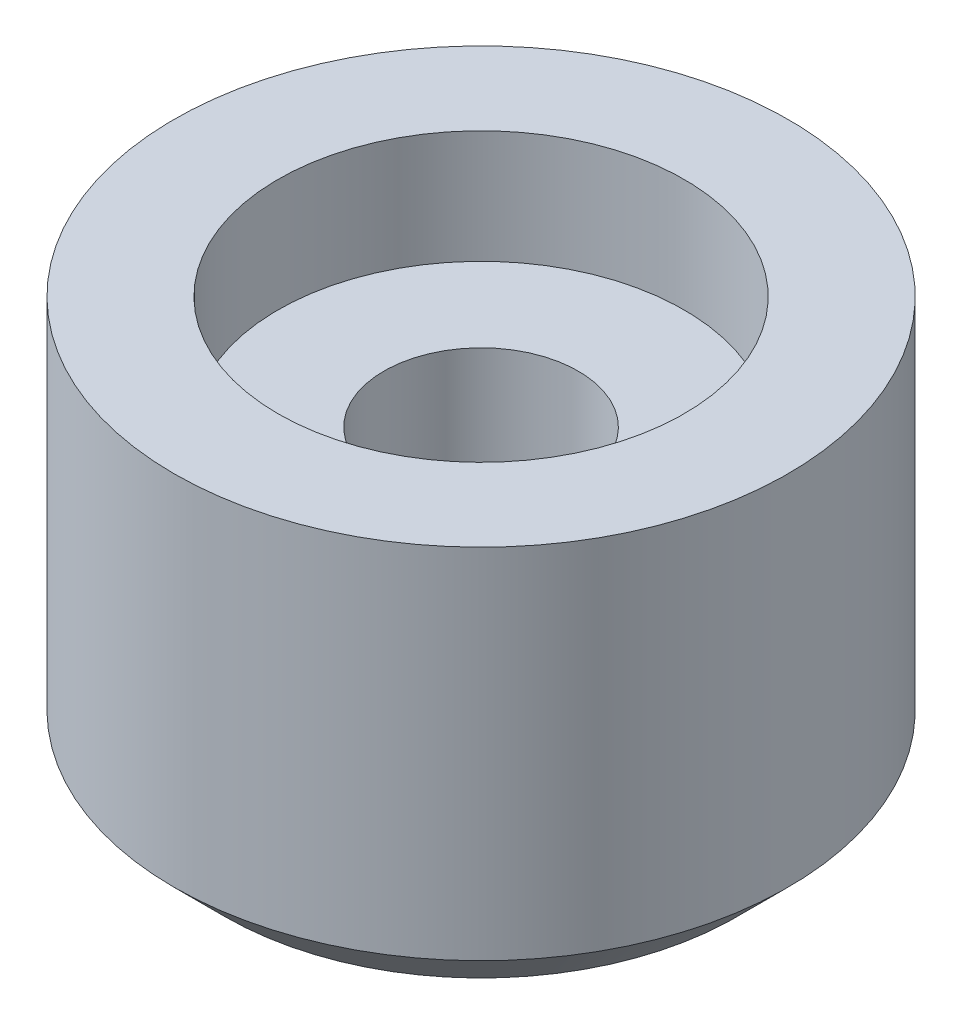
SolidWorks part; units mm, degrees
ref_plane "Front Plane" through (0, 0, 0) normal (0, 0, 1) x (1, 0, 0)
ref_plane "Top Plane" through (0, 0, 0) normal (0, 1, 0) x (1, 0, 0)
ref_plane "Right Plane" through (0, 0, 0) normal (1, 0, 0) x (0, 0, -1)
sketch "Sketch1" plane through (0, 0, 0) normal (0, 1, 0) x (1, 0, 0)
  circle A0 centre (0, 0) radius 6
  dimension "D1" = 12
extrude "Boss-Extrude1" add sketch "Sketch1" along normal blind 8
hole_wizard "CBORE for #6 Binding Head Machine Screw2" positions "Sketch2" profile "Sketch3" counterbore size "#6" standard "ANSI Inch" end condition through all
sketch "Sketch2" plane through (0, 8, 0) normal (0, 1, 0) x (1, 0, 0)
  point P0 (0, 0)
sketch "Sketch3" plane through (0, 8, 0) normal (1, 0, 0) x (0, 0, 1)
  line L0 (0, 0) -> (0, 8)
  line L1 (0, 8) -> (1.8986, 8)
  line L3 (1.8986, 8) -> (1.8986, 2.2098)
  line L4 (1.8986, 2.2098) -> (3.9688, 2.2098)
  line L5 (3.9688, 2.2098) -> (3.9688, 0)
  line L7 (3.9688, 0) -> (0, 0)
  line L11 (0, -6.35) -> (0, 107.95) construction
  dimension "Thru Hole Dia." = 3.7973
  dimension "Thru Hole Depth" = 8
  dimension "C'Bore Dia." = 7.9375
  dimension "C'Bore Depth" = 2.2098
chamfer "Chamfer1" distance 1 angle 45 1 edges at (0, 0, 6)
